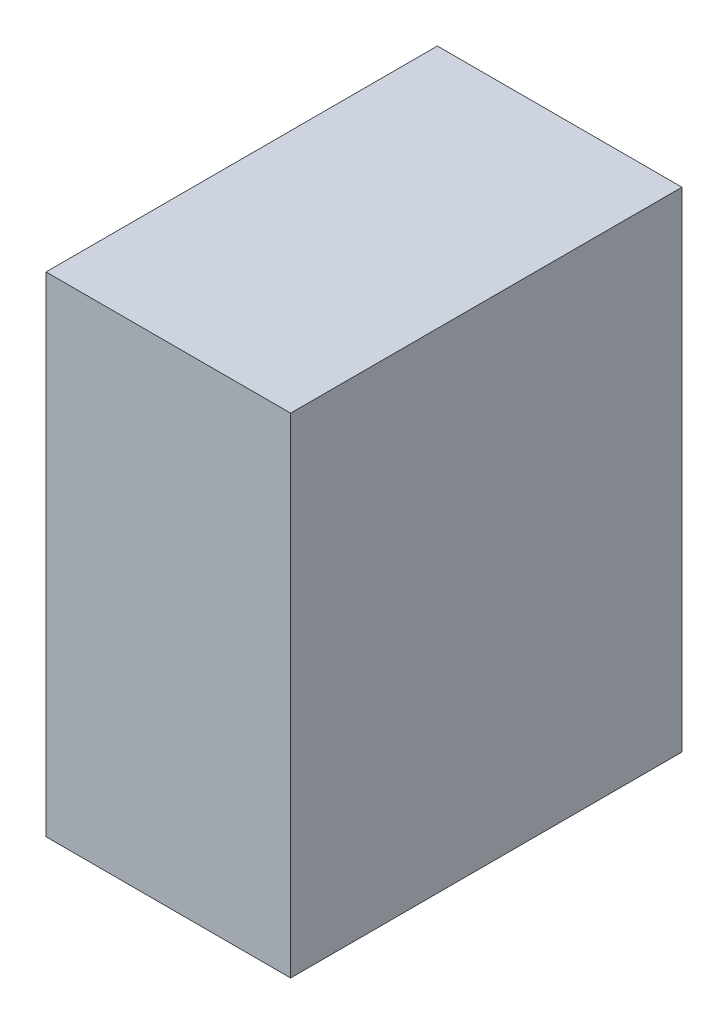
SolidWorks part; units mm, degrees
ref_plane "Front Plane" through (0, 0, 0) normal (0, 0, 1) x (1, 0, 0)
ref_plane "Top Plane" through (0, 0, 0) normal (0, 1, 0) x (1, 0, 0)
ref_plane "Right Plane" through (0, 0, 0) normal (1, 0, 0) x (0, 0, -1)
sketch "Sketch1" plane through (0, 0, 0) normal (0, 0, 1) x (1, 0, 0)
  line L1 (-50, 53.6184) -> (0, 53.6184)
  line L2 (-50, 53.6184) -> (-50, -46.3816)
  line L3 (-50, -46.3816) -> (0, -46.3816)
  line L4 (0, 53.6184) -> (0, -46.3816)
  dimension "D1" = 100
  dimension "D2" = 50
extrude "Boss-Extrude1" add sketch "Sketch1" along normal blind 80
